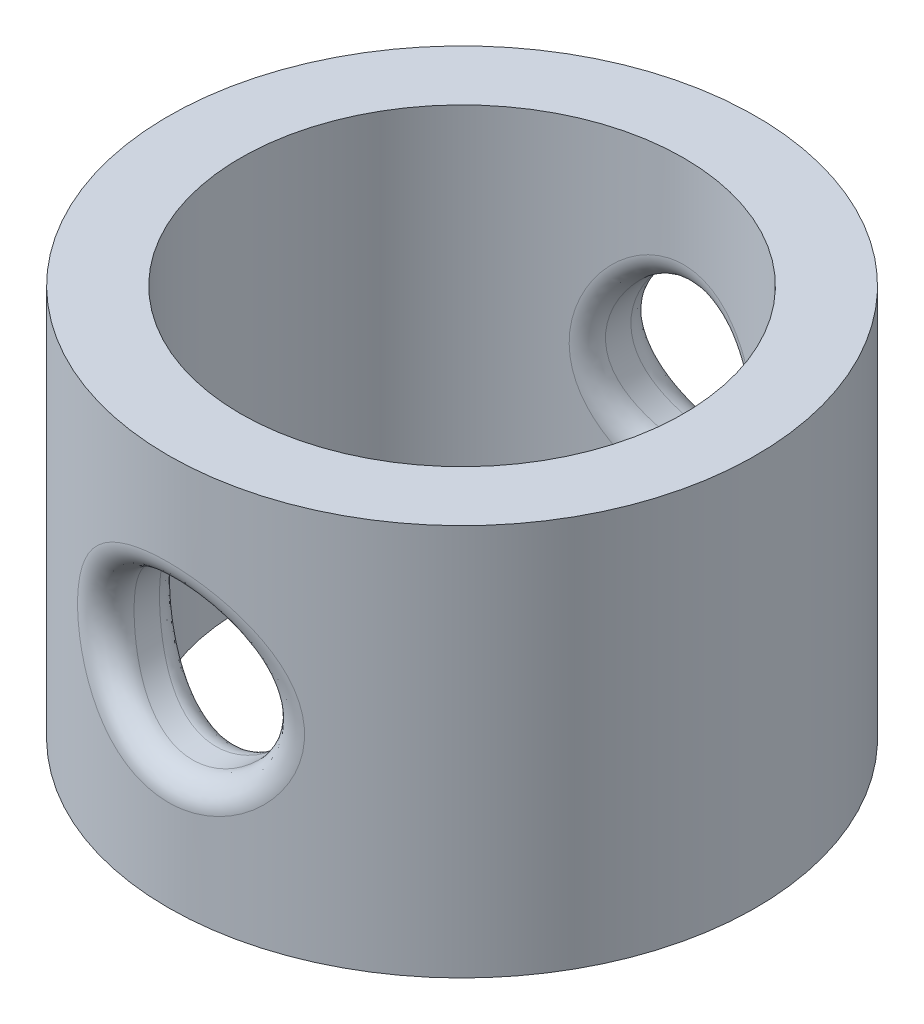
SolidWorks part; units mm, degrees
ref_plane "Front Plane" through (0, 0, 0) normal (0, 0, 1) x (1, 0, 0)
ref_plane "Top Plane" through (0, 0, 0) normal (0, 1, 0) x (1, 0, 0)
ref_plane "Right Plane" through (0, 0, 0) normal (1, 0, 0) x (0, 0, -1)
sketch "Sketch1" plane through (0, 0, 0) normal (0, 1, 0) x (1, 0, 0)
  circle A0 centre (0, 0) radius 6
  circle A1 centre (0, 0) radius 4.525
  dimension "D1" = 12
  dimension "D2" = 9.05
extrude "Boss-Extrude1" add sketch "Sketch1" along normal blind 8
sketch "Sketch2" plane through (0, 0, 0) normal (0, 0, 1) x (1, 0, 0)
  line L0 (0, -0.4138) -> (0, 8.3889) construction
  circle A0 centre (0, 3.9875) radius 1.625
  dimension "D1" = 3.25
extrude "Cut-Extrude1" cut sketch "Sketch2" against normal through all both and the other way through all
fillet "Fillet1" radius 0.5 4 edges at (0.2612, 2.3836, -4.5175) (-1.6035, 4.2509, 4.2314) (0.3084, 2.3921, -5.9921) (-1.5953, 4.2965, 5.784)
